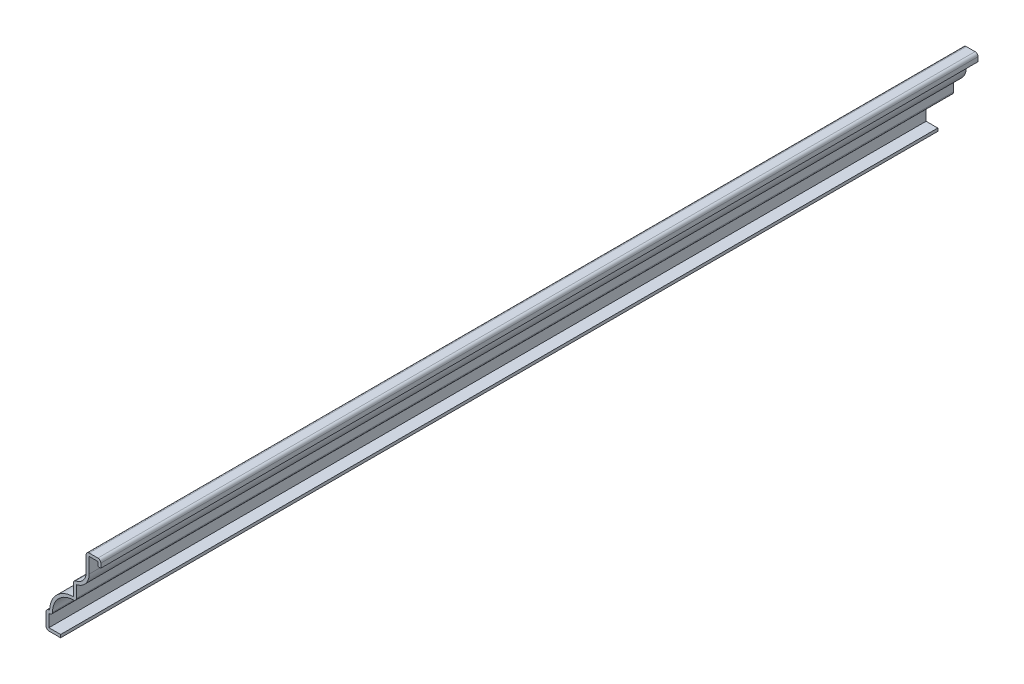
SolidWorks part; units mm, degrees
ref_plane "Front Plane" through (0, 0, 0) normal (0, 0, 1) x (1, 0, 0)
ref_plane "Top Plane" through (0, 0, 0) normal (0, 1, 0) x (1, 0, 0)
ref_plane "Right Plane" through (0, 0, 0) normal (1, 0, 0) x (0, 0, -1)
sketch "Sketch1" plane through (0, 0, 0) normal (0, 0, 1) x (1, 0, 0)
  line L0 (0, 0) -> (-17.4625, 0) construction
  line L1 (-17.4625, 0) -> (-23.8125, 0)
  line L2 (-23.8125, 0) -> (-23.8125, 7.9375)
  line L3 (-23.8125, 7.9375) -> (-22.225, 7.9375)
  line L4 (-11.9062, 18.2562) -> (-11.9062, 24.6062)
  line L5 (-6.35, 30.1625) -> (-6.35, 38.1)
  line L6 (-6.35, 38.1) -> (0, 38.1)
  line L7 (0, 38.1) -> (0, 34.925)
  line L8 (0, 34.925) -> (0, 0) construction
  arc A0 (-22.225, 7.9375) -> (-11.9062, 18.2562) centre (-11.9063, 7.9375) cw
  arc A1 (-11.9062, 24.6062) -> (-6.35, 30.1625) centre (-11.9062, 30.1625) ccw
  dimension "D5" = 10.3187
  dimension "D6" = 5.5562
  dimension "D1" = 38.1
  dimension "D2" = 7.9375
  dimension "D3" = 10.3187
  dimension "D4" = 6.35
  dimension "D7" = 3.175
  dimension "D8" = 6.35
  dimension "D9" = 5.5562
  dimension "D10" = 10.3187
  dimension "D11" = 1.5875
  dimension "D12" = 6.35
extrude "Extrude-Thin1" add sketch "Sketch1" against normal blind 381 thin
fillet "Fillet1" radius 1.27 7 edges at (-23.8125, 0, -190.5) (-23.8125, 7.9375, -190.5) (-20.8654, 6.6675, -190.5) (-10.6363, 16.8967, -190.5) (-6.35, 38.1, -190.5) (-11.9062, 24.6062, -190.5) (0, 38.1, -190.5)
